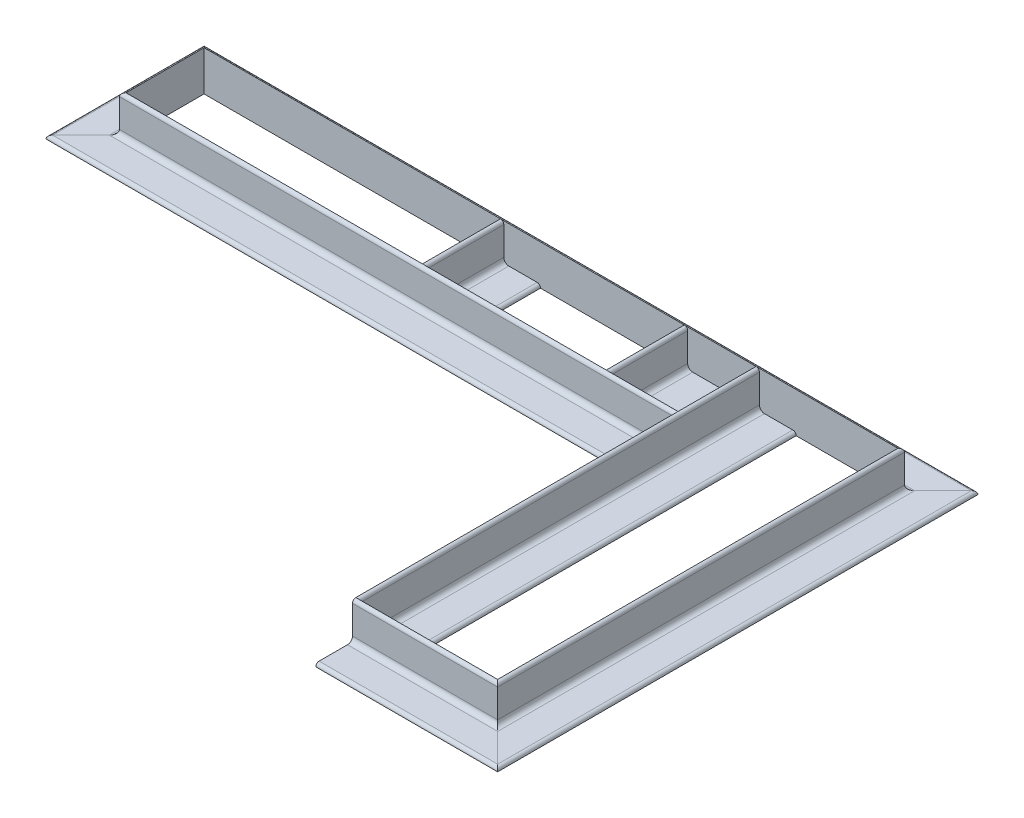
SolidWorks part; units mm, degrees
material "6061-T6 (SS)"
ref_plane "Front Plane" through (0, 0, 0) normal (0, 0, 1) x (1, 0, 0)
ref_plane "Top Plane" through (0, 0, 0) normal (0, 1, 0) x (1, 0, 0)
ref_plane "Right Plane" through (0, 0, 0) normal (1, 0, 0) x (0, 0, -1)
sketch "Sketch1" plane through (0, 0, 0) normal (0, 1, 0) x (1, 0, 0)
  line L1 (-330.2, 190.5) -> (330.2, 190.5)
  line L2 (-330.2, 190.5) -> (-330.2, 116.2203)
  line L3 (330.2, -190.5) -> (195.2, -190.5)
  line L4 (330.2, 190.5) -> (330.2, -190.5)
  line L5 (-330.2, 190.5) -> (-201.4486, 116.2203) construction
  line L6 (-330.2, -190.5) -> (330.2, 190.5) construction
  line L7 (126.8794, 190.5) -> (126.8794, 116.2203)
  line L8 (-48.1206, 190.5) -> (-48.1206, 116.2203)
  line L9 (195.2, 190.5) -> (195.2, -190.5)
  line L10 (330.2, -67.3655) -> (195.2, -67.3655)
  line L11 (195.2, 116.2203) -> (-330.2, 116.2203)
  line L12 (-201.4486, 116.2203) -> (330.2, -190.5) construction
  point P0 (0, 0)
  dimension "D1" = 381
  dimension "D2" = 660.4
  dimension "D4" = 175
  dimension "D5" = 135
  dimension "D6" = 74.2797
  dimension "D7" = 257.8655
  dimension "D8" = 381
  dimension "D9" = 660.4
other "Structural Member4"
ref_plane "Plane4" through (330.2, 0, -190.5) normal (0, 0, 1) x (1, 0, 0)
sketch "Sketch114" plane through (330.2, 0, -190.5) normal (0, 0, 1) x (1, 0, 0)
  line L0 (0, 0) -> (0, 38.1)
  line L1 (0, 38.1) -> (0.0051, 38.1)
  line L2 (3.175, 34.9301) -> (3.175, 7.9502)
  line L3 (7.9502, 3.175) -> (34.9301, 3.175)
  line L4 (38.1, 0.0051) -> (38.1, 0)
  line L5 (38.1, 0) -> (0, 0)
  arc A0 (38.1, 0.0051) -> (34.9301, 3.175) centre (34.9301, 0.0051) ccw
  arc A1 (0.0051, 38.1) -> (3.175, 34.9301) centre (0.0051, 34.9301) cw
  arc A2 (7.9502, 3.175) -> (3.175, 7.9502) centre (7.9502, 7.9502) cw
  circle A3 centre (0, 0) radius 3.175 construction
  point P10 (0, 19.05)
  point P14 (19.05, 0)
  point P15 (0, 0)
  dimension "D2" = 0.0051
  dimension "Radius_1" = 4.7752
  dimension "Radius_2" = 3.175
  dimension "D1" = 3.175
  dimension "V_leg" = 38.1
  dimension "H_leg" = 38.1
  dimension "Thickness" = 3.175
  dimension "Flat_wid" = 0.0051
other "Structural Member5"
ref_plane "Plane5" through (195.2, 0, -190.5) normal (0, 0, 1) x (1, 0, 0)
sketch "Sketch115" plane through (195.2, 0, -190.5) normal (0, 0, 1) x (1, 0, 0)
  line L0 (0, 0) -> (0, 38.1)
  line L1 (0, 38.1) -> (0.0051, 38.1)
  line L2 (3.175, 34.9301) -> (3.175, 7.9502)
  line L3 (7.9502, 3.175) -> (34.9301, 3.175)
  line L4 (38.1, 0.0051) -> (38.1, 0)
  line L5 (38.1, 0) -> (0, 0)
  arc A0 (38.1, 0.0051) -> (34.9301, 3.175) centre (34.9301, 0.0051) ccw
  arc A1 (0.0051, 38.1) -> (3.175, 34.9301) centre (0.0051, 34.9301) cw
  arc A2 (7.9502, 3.175) -> (3.175, 7.9502) centre (7.9502, 7.9502) cw
  circle A3 centre (0, 0) radius 3.175 construction
  point P10 (0, 19.05)
  point P14 (19.05, 0)
  point P15 (0, 0)
  dimension "D2" = 0.0051
  dimension "Radius_1" = 4.7752
  dimension "Radius_2" = 3.175
  dimension "D1" = 3.175
  dimension "V_leg" = 38.1
  dimension "H_leg" = 38.1
  dimension "Thickness" = 3.175
  dimension "Flat_wid" = 0.0051
